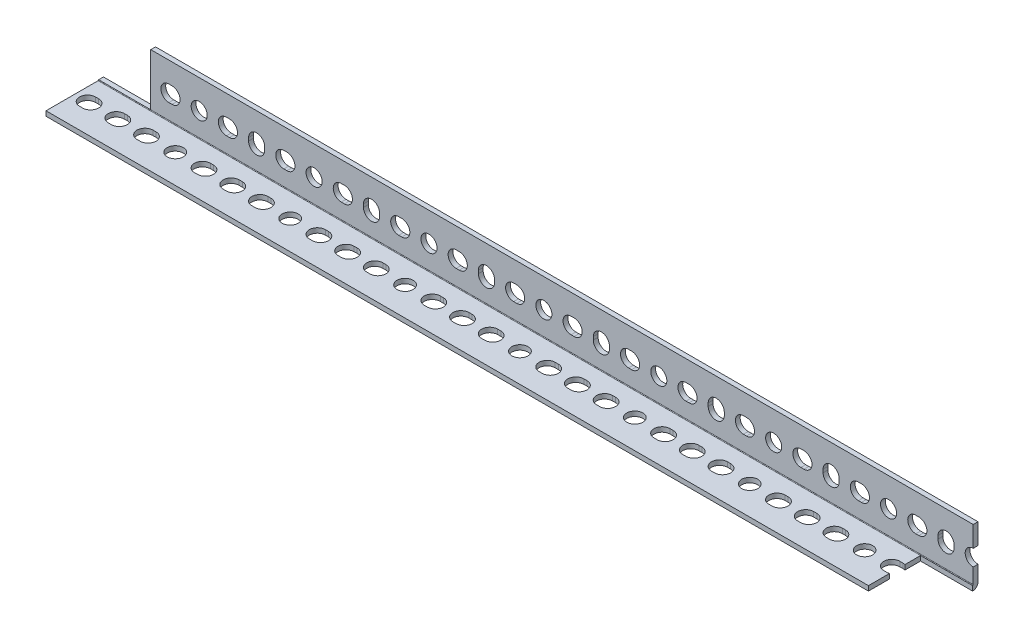
SolidWorks part; units mm, degrees
ref_plane "Front Plane" through (0, 0, 0) normal (0, 0, 1) x (1, 0, 0)
ref_plane "Top Plane" through (0, 0, 0) normal (0, 1, 0) x (1, 0, 0)
ref_plane "Right Plane" through (0, 0, 0) normal (1, 0, 0) x (0, 0, -1)
sketch "Sketch1" plane through (0, 0, 0) normal (1, 0, 0) x (0, 0, -1)
  line L0 (-19.05, -15.875) -> (15.875, -15.875) construction
  line L1 (15.875, -15.875) -> (15.875, 19.05) construction
  line L2 (15.875, 19.05) -> (19.05, 19.05) construction
  line L3 (19.05, 19.05) -> (19.05, -19.05) construction
  line L4 (19.05, -19.05) -> (-19.05, -19.05) construction
  line L5 (-19.05, -19.05) -> (-19.05, -15.875) construction
  line L6 (0, -19.05) -> (0, 19.05) construction
  line L7 (19.05, 0) -> (-19.05, 0) construction
  arc A0 (15.494, -15.875) -> (15.875, -15.494) centre (15.494, -15.494) ccw construction
  dimension "D1" = 0.381
  dimension "Thickness | T" = 3.175
  dimension "Width (B)" = 38.1
  dimension "Width (A)" = 38.1
sketch "Sketch2" plane through (0, 0, 0) normal (0, 0, 1) x (1, 0, 0)
  line L0 (-1219.2, 0) -> (1219.2, 0) construction
  line L1 (-1219.2, 19.05) -> (1219.2, 19.05) construction
  line L2 (-1219.2, 19.05) -> (-1219.2, -19.05) construction
  line L3 (-1219.2, -19.05) -> (1219.2, -19.05) construction
  line L4 (1219.2, 19.05) -> (1219.2, -19.05) construction
  line L5 (0, 19.05) -> (0, -19.05) construction
  line L6 (1191.641, 0) -> (1189.609, 0) construction
  line L7 (-1219.2, -15.875) -> (1219.2, -15.875) construction
  line L8 (1191.641, -5.334) -> (1189.609, -5.334) construction
  line L9 (1191.641, 5.334) -> (1189.609, 5.334) construction
  line L10 (1171.575, -1.016) -> (1171.575, 1.016) construction
  line L11 (1166.241, -1.016) -> (1166.241, 1.016) construction
  line L12 (1176.909, -1.016) -> (1176.909, 1.016) construction
  line L14 (1153.541, 0) -> (1151.509, 0) construction
  line L15 (1153.541, -5.334) -> (1151.509, -5.334) construction
  line L16 (1153.541, 5.334) -> (1151.509, 5.334) construction
  circle A0 centre (1209.675, 0) radius 5.334 construction
  arc A2 (1191.641, -5.334) -> (1191.641, 5.334) centre (1191.641, 0) ccw construction
  arc A3 (1189.609, 5.334) -> (1189.609, -5.334) centre (1189.609, 0) ccw construction
  arc A4 (1166.241, -1.016) -> (1176.909, -1.016) centre (1171.575, -1.016) ccw construction
  arc A5 (1176.909, 1.016) -> (1166.241, 1.016) centre (1171.575, 1.016) ccw construction
  arc A6 (1153.541, -5.334) -> (1153.541, 5.334) centre (1153.541, 0) ccw construction
  arc A7 (1151.509, 5.334) -> (1151.509, -5.334) centre (1151.509, 0) ccw construction
  point P15 (1123.95, 0)
  point P16 (-1123.95, 0)
  point P17 (1190.625, 0)
  point P24 (1215.009, 0)
  point P26 (1171.575, 0)
  point P37 (1152.525, 0)
  dimension "Mounting Hole Diameter" = 10.668
  dimension "Length | L" = 2438.4
  dimension "D1" = 9.525
  dimension "D2" = 85.725
  dimension "D3" = 12.7
  dimension "D4" = 19.05
  dimension "Mounting Hole Center to Center" = 19.05
  dimension "D5" = 19.05
  dimension "D7" = 19.05
sketch "Sketch3" plane through (0, 0, 0) normal (0, 1, 0) x (1, 0, 0)
  line L0 (1191.641, 0) -> (1189.609, 0) construction
  line L1 (-1219.2, 19.05) -> (1219.2, 19.05) construction
  line L2 (-1219.2, 19.05) -> (-1219.2, -19.05) construction
  line L3 (-1219.2, -19.05) -> (1219.2, -19.05) construction
  line L4 (1219.2, 19.05) -> (1219.2, -19.05) construction
  line L5 (-1219.2, 15.875) -> (1219.2, 15.875) construction
  line L6 (1191.641, -5.334) -> (1189.609, -5.334) construction
  line L7 (1170.559, 0) -> (1172.591, 0) construction
  line L8 (1191.641, 5.334) -> (1189.609, 5.334) construction
  line L12 (1151.509, 0) -> (1153.541, 0) construction
  line L13 (1151.509, 5.334) -> (1153.541, 5.334) construction
  line L14 (1151.509, -5.334) -> (1153.541, -5.334) construction
  line L16 (1191.641, 5.334) -> (1209.675, 5.334) construction
  line L17 (1170.559, 5.334) -> (1172.591, 5.334) construction
  line L18 (1170.559, -5.334) -> (1172.591, -5.334) construction
  circle A0 centre (1209.675, 0) radius 5.334 construction
  arc A2 (1191.641, -5.334) -> (1191.641, 5.334) centre (1191.641, 0) ccw construction
  arc A3 (1189.609, 5.334) -> (1189.609, -5.334) centre (1189.609, 0) ccw construction
  arc A6 (1151.509, 5.334) -> (1151.509, -5.334) centre (1151.509, 0) ccw construction
  arc A7 (1153.541, -5.334) -> (1153.541, 5.334) centre (1153.541, 0) ccw construction
  arc A10 (1170.559, 5.334) -> (1170.559, -5.334) centre (1170.559, 0) ccw construction
  arc A11 (1172.591, -5.334) -> (1172.591, 5.334) centre (1172.591, 0) ccw construction
  point P9 (1190.625, 0)
  point P21 (1215.009, 0)
  point P28 (1171.575, 0)
  point P42 (1152.525, 0)
  dimension "D1" = 19.05
sketch "Sketch4" plane through (0, 0, 0) normal (1, 0, 0) x (0, 0, -1)
  line L0 (-19.05, -15.875) -> (15.494, -15.875)
  line L1 (15.875, -15.494) -> (15.875, 19.05)
  line L2 (15.875, 19.05) -> (19.05, 19.05)
  line L3 (19.05, 19.05) -> (19.05, -15.494)
  line L4 (15.494, -19.05) -> (-19.05, -19.05)
  line L5 (-19.05, -19.05) -> (-19.05, -15.875)
  arc A0 (15.494, -15.875) -> (15.875, -15.494) centre (15.494, -15.494) ccw
  arc A1 (19.05, -15.494) -> (15.494, -19.05) centre (15.494, -15.494) cw
extrude "Boss-Extrude1" add sketch "Sketch4" along normal up to vertex (1219.2 mm away) and the other way up to vertex (1219.2 mm away) up to point (1219.2, 0, 0) other way up to point (-1219.2, 0, 0)
sketch "Sketch5" plane through (0, 0, 0) normal (0, 0, 1) x (1, 0, 0)
  line L0 (1189.609, 0) -> (1191.641, 0) construction
  line L1 (1189.609, 5.334) -> (1191.641, 5.334)
  line L2 (1189.609, -5.334) -> (1191.641, -5.334)
  line L3 (1171.575, 1.016) -> (1171.575, -1.016) construction
  line L4 (1176.909, 1.016) -> (1176.909, -1.016)
  line L5 (1166.241, 1.016) -> (1166.241, -1.016)
  line L6 (1151.509, 0) -> (1153.541, 0) construction
  line L7 (1151.509, 5.334) -> (1153.541, 5.334)
  line L8 (1151.509, -5.334) -> (1153.541, -5.334)
  circle A0 centre (1209.675, 0) radius 5.334
  arc A1 (1189.609, 5.334) -> (1189.609, -5.334) centre (1189.609, 0) ccw
  arc A2 (1191.641, -5.334) -> (1191.641, 5.334) centre (1191.641, 0) ccw
  arc A3 (1176.909, 1.016) -> (1166.241, 1.016) centre (1171.575, 1.016) ccw
  arc A4 (1166.241, -1.016) -> (1176.909, -1.016) centre (1171.575, -1.016) ccw
  arc A5 (1151.509, 5.334) -> (1151.509, -5.334) centre (1151.509, 0) ccw
  arc A6 (1153.541, -5.334) -> (1153.541, 5.334) centre (1153.541, 0) ccw
  point P5 (1190.625, 0)
  point P13 (1171.575, 0)
  point P28 (1152.525, 0)
extrude "Cut-Extrude1" cut sketch "Sketch5" against normal through all
pattern_linear "LPattern1" count 33 spacing 76.2 along (-1, 0, 0) of "Cut-Extrude1"
sketch "Sketch6" plane through (0, 0, 0) normal (0, 1, 0) x (1, 0, 0)
  line L0 (1189.609, 0) -> (1191.641, 0) construction
  line L1 (1189.609, 5.334) -> (1191.641, 5.334)
  line L2 (1189.609, -5.334) -> (1191.641, -5.334)
  line L3 (1170.559, 0) -> (1172.591, 0) construction
  line L6 (1151.509, 0) -> (1153.541, 0) construction
  line L7 (1151.509, 5.334) -> (1153.541, 5.334)
  line L8 (1151.509, -5.334) -> (1153.541, -5.334)
  line L11 (1170.559, 5.334) -> (1172.591, 5.334)
  line L12 (1170.559, -5.334) -> (1172.591, -5.334)
  circle A0 centre (1209.675, 0) radius 5.334
  arc A1 (1189.609, 5.334) -> (1189.609, -5.334) centre (1189.609, 0) ccw
  arc A2 (1191.641, -5.334) -> (1191.641, 5.334) centre (1191.641, 0) ccw
  arc A5 (1151.509, 5.334) -> (1151.509, -5.334) centre (1151.509, 0) ccw
  arc A6 (1153.541, -5.334) -> (1153.541, 5.334) centre (1153.541, 0) ccw
  arc A9 (1170.559, 5.334) -> (1170.559, -5.334) centre (1170.559, 0) ccw
  arc A10 (1172.591, -5.334) -> (1172.591, 5.334) centre (1172.591, 0) ccw
  point P8 (1190.625, 0)
  point P15 (1171.575, 0)
  point P22 (1152.525, 0)
extrude "Cut-Extrude2" cut sketch "Sketch6" against normal through all
pattern_linear "LPattern2" count 33 spacing 76.2 along (-1, 0, 0) of "Cut-Extrude2"
sketch "Sketch7" plane through (0, 0, -15.875) normal (0, 0, 1) x (1, 0, 0)
  line L0 (-1219.2, 1.778) -> (1219.2, 1.778) construction
  line L1 (-1219.2, 19.05) -> (-1219.2, -15.494) construction
  line L2 (1219.2, 19.05) -> (1219.2, -15.494) construction
  line L3 (1219.2, -19.05) -> (-1219.2, -19.05) construction
  line L4 (3077.6, 22.606) -> (-639.2, 22.606)
  line L5 (3077.6, 22.606) -> (3077.6, -19.05)
  line L6 (3077.6, -19.05) -> (-639.2, -19.05)
  line L7 (-639.2, 22.606) -> (-639.2, -19.05)
  line L8 (3077.6, 22.606) -> (-639.2, -19.05) construction
  line L9 (3077.6, -19.05) -> (-639.2, 22.606) construction
  dimension "D1" = 3716.8
extrude "Cut-Extrude3" cut sketch "Sketch7" against normal through all both and the other way through all
sketch "Sketch8" plane through (0, 0, -15.875) normal (0, 0, 1) x (1, 0, 0)
  line L0 (-639.2, -15.494) -> (-1219.2, -15.494) construction
  line L1 (-1219.2, 19.05) -> (-1184.656, 19.05)
  line L2 (-1219.2, 19.05) -> (-1219.2, -15.494)
  line L3 (-1219.2, -15.494) -> (-1184.656, -15.494)
  line L4 (-1184.656, 19.05) -> (-1184.656, -15.494)
  dimension "D1" = 34.544
extrude "Cut-Extrude4" cut sketch "Sketch8" against normal through all both and the other way through all
sketch "Sketch9" plane through (0, -19.05, 0) normal (0, -1, 0) x (1, 0, 0)
  line L0 (-639.2, -15.494) -> (-1219.2, -15.494) construction
  line L1 (-639.2, 19.05) -> (-673.744, 19.05)
  line L2 (-639.2, 19.05) -> (-639.2, -15.494)
  line L3 (-639.2, -15.494) -> (-673.744, -15.494)
  line L4 (-673.744, 19.05) -> (-673.744, -15.494)
  dimension "D1" = 34.544
extrude "Cut-Extrude5" cut sketch "Sketch9" against normal through all both and the other way through all
equation "\"D1@Sketch2\"= ( \"Length | L@Sketch2\" - \"Mounting Hole Center to Center@Sketch2\" * \"Num Holes\" ) / 2"
equation "\"Num Holes\"= int ( \"Length | L@Sketch2\" / \"Mounting Hole Center to Center@Sketch2\" ) - 1"
equation "\"D2@Sketch2\"=\"Mounting Hole Center to Center@Sketch2\"*4.5"
equation "\"D3@LPattern1\"=\"Mounting Hole Center to Center@Sketch2\"*4"
equation "\"D4@Sketch2\"=\"Mounting Hole Center to Center@Sketch2\""
equation "\"D3@LPattern2\"=\"Mounting Hole Center to Center@Sketch2\"*4"
equation "\"D7@Sketch2\"=\"Mounting Hole Center to Center@Sketch2\""
